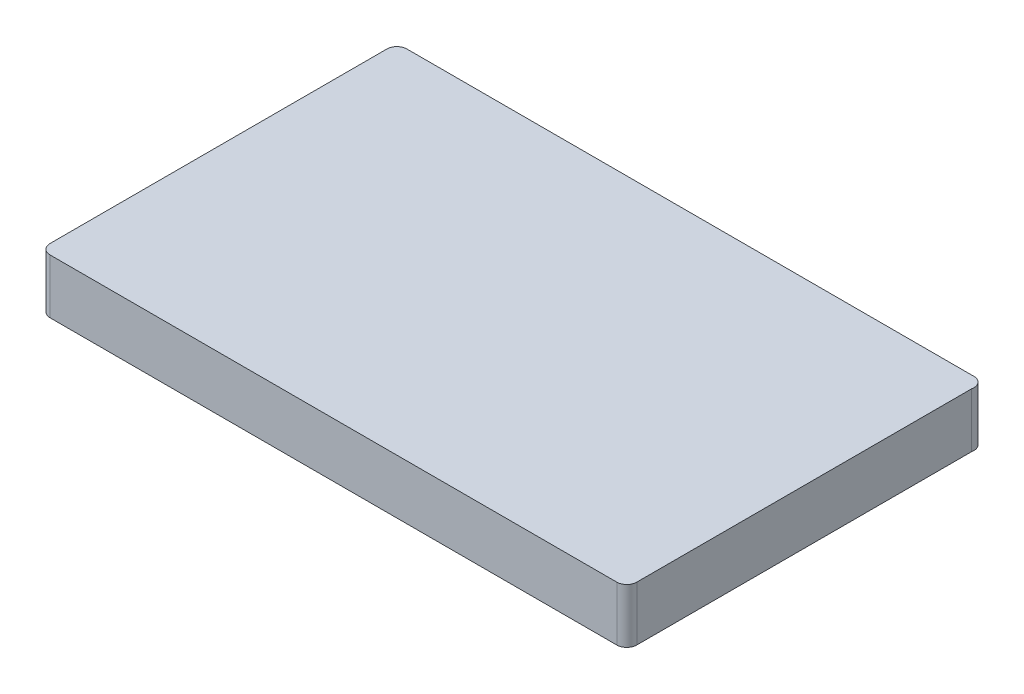
SolidWorks part; units mm, degrees
ref_plane "Front Plane" through (0, 0, 0) normal (0, 0, 1) x (1, 0, 0)
ref_plane "Top Plane" through (0, 0, 0) normal (0, 1, 0) x (1, 0, 0)
ref_plane "Right Plane" through (0, 0, 0) normal (1, 0, 0) x (0, 0, -1)
sketch "Sketch1" plane through (0, 0, 0) normal (0, 1, 0) x (1, 0, 0)
  line L0 (68.6023, 41.7214) -> (-72.5778, -44.1392) construction
  line L1 (71, -44.7) -> (-71, -44.7)
  line L2 (73.5, -42.2) -> (73.5, 41.7174)
  line L3 (70.7167, 44.7) -> (-71, 44.7)
  line L4 (-73.5, -42.2) -> (-73.5, 42.2)
  line L5 (72.5778, -44.1392) -> (-72.5778, 44.1392) construction
  arc A0 (73.5, 41.7174) -> (70.7167, 44.7) centre (71.0516, 42.2225) ccw
  arc A1 (71, -44.7) -> (73.5, -42.2) centre (71, -42.2) ccw
  arc A2 (-73.5, -42.2) -> (-71, -44.7) centre (-71, -42.2) ccw
  arc A3 (-71, 44.7) -> (-73.5, 42.2) centre (-71, 42.2) ccw
  point P0 (0, 0)
  dimension "D3" = 5
  dimension "D1" = 147
  dimension "D2" = 89.4
extrude "Boss-Extrude1" add sketch "Sketch1" along normal blind 13.65
